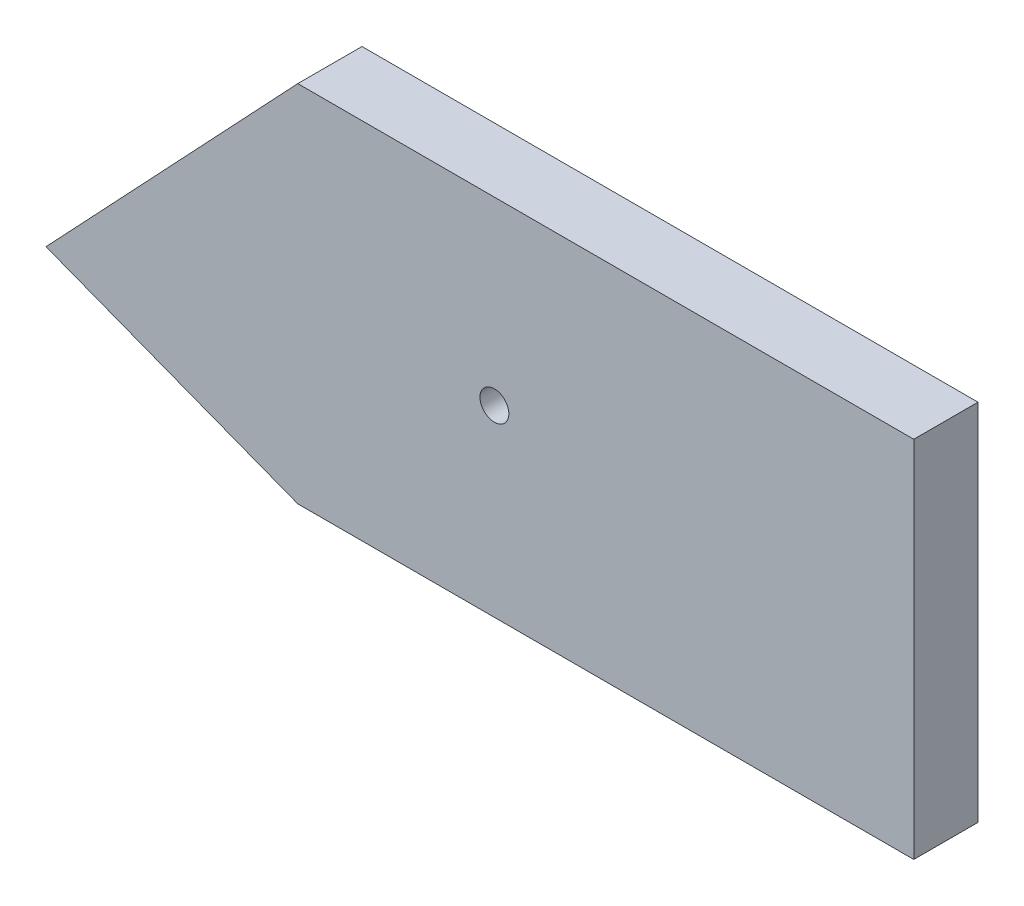
SolidWorks part; units mm, degrees
ref_plane "XY" through (0, 0, 0) normal (0, 0, 1) x (1, 0, 0)
ref_plane "XZ" through (0, 0, 0) normal (0, 1, 0) x (1, 0, 0)
ref_plane "YZ" through (0, 0, 0) normal (1, 0, 0) x (0, 0, -1)
sketch "ref externes" plane through (0, 0, 129.9356) normal (0, 0, 1) x (1, 0, 0)
  line L0 (-556.8868, -138.2683) -> (-596.0822, -179.8523)
  line L1 (-596.0822, -179.8523) -> (-556.8868, -194.929)
  line L4 (-460.9794, -138.2683) -> (-556.8868, -138.2683)
  line L5 (-556.8868, -138.2683) -> (-556.8868, -194.929)
  line L6 (-556.8868, -194.929) -> (-460.9794, -194.929)
  line L7 (-460.9794, -194.929) -> (-460.9794, -138.2683)
  line L8 (-460.9794, -138.2683) -> (-556.8868, -138.2683)
  line L10 (-556.8868, -194.929) -> (-460.9794, -194.929)
  line L11 (-460.9794, -194.929) -> (-460.9794, -138.2683)
  dimension "D2" = 39.1954
  dimension "D3" = 15.0767
  dimension "D1" = 0
sketch "ref externes (internes)" plane through (0, 0, 0) normal (0, 0, 1) x (1, 0, 0)
  line L0 (-556.8868, -138.2683) -> (-556.8868, -194.929) construction
  line L8 (-460.9794, -138.2683) -> (-556.8868, -138.2683)
  line L10 (-556.8868, -194.929) -> (-460.9794, -194.929)
  line L11 (-460.9794, -194.929) -> (-460.9794, -138.2683)
  line L20 (-460.9794, -138.2683) -> (-556.8868, -138.2683)
  line L22 (-556.8868, -194.929) -> (-460.9794, -194.929)
  line L23 (-460.9794, -194.929) -> (-460.9794, -138.2683)
  line L25 (-556.8868, -138.2683) -> (-596.0822, -179.8523)
  line L26 (-556.8868, -138.2683) -> (-596.0822, -179.8523)
  line L27 (-596.0822, -179.8523) -> (-556.8868, -194.929)
  line L28 (-596.0822, -179.8523) -> (-556.8868, -194.929)
  dimension "D1" = 0
extrude "Boss.-Extru.1" add sketch "ref externes (internes)" along normal blind 10
hole_wizard "Dégagement M42" positions "Esquisse14" profile "Esquisse15" hole size "M4" standard "ISO" end condition through all
sketch "Esquisse14" plane through (0, 0, 10) normal (0, 0, 1) x (1, 0, 0)
  line L1 (-556.5921, -142.2934) -> (-526.2713, -166.3649) construction
  line L2 (-526.2713, -166.3649) -> (-526.2713, -142.2934) construction
  line L3 (-556.5921, -142.2934) -> (-460.6846, -142.2934) construction
  line L4 (-526.2713, -142.2934) -> (-556.5921, -142.2934) construction
  point P0 (-526.2713, -166.3649)
  dimension "D1" = 38.7142
  dimension "D2" = 38.446
sketch "Esquisse15" plane through (-526.2713, -166.3649, 10) normal (1, 0, 0) x (0, -1, 0)
  line L0 (0, 0) -> (0, 10)
  line L1 (0, 10) -> (2.25, 10)
  line L2 (2.25, 10) -> (2.25, 0)
  line L5 (2.25, 0) -> (0, 0)
  line L11 (0, -6.35) -> (0, 107.95) construction
  dimension "Diamètre du perçage jusqu'au prochain" = 4.5
  dimension "Profondeur du perçage jusqu'au prochain" = 10
sketch "Sketch1" plane through (0, 0, 10) normal (0, 0, 1) x (1, 0, 0)
  line L0 (-460.9794, -138.2683) -> (-556.8868, -138.2683) construction
  line L1 (-460.9794, -138.2683) -> (-556.8868, -138.2683)
  circle A0 centre (-526.2713, -166.3649) radius 2.25 construction
  circle A1 centre (-526.2713, -166.3649) radius 2.25
  dimension "D1" = 95.9074
